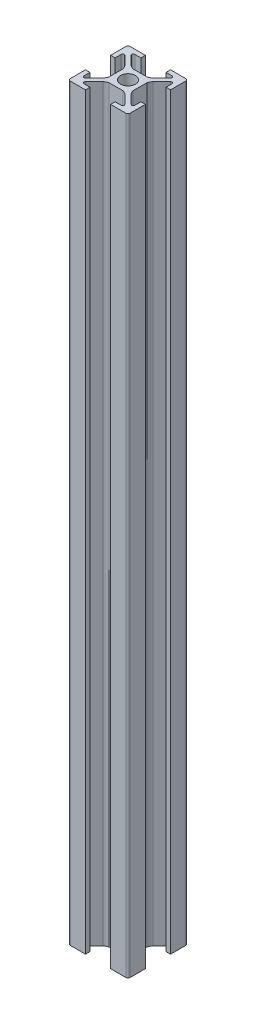
SolidWorks part; units mm, degrees
ref_plane "Front Plane" through (0, 0, 0) normal (0, 0, 1) x (1, 0, 0)
ref_plane "Top Plane" through (0, 0, 0) normal (0, 1, 0) x (1, 0, 0)
ref_plane "Right Plane" through (0, 0, 0) normal (1, 0, 0) x (0, 0, -1)
sketch "Sketch1" plane through (0, 0, 0) normal (0, 1, 0) x (1, 0, 0)
  line L0 (-3.611, 4.6716) -> (-6.5858, 7.6464)
  line L1 (9.25, -10) -> (4.2, -10)
  line L2 (10, -9.25) -> (10, -4.2)
  line L3 (9.25, 10) -> (4.2, 10)
  line L4 (-10, -9.25) -> (-10, -4.2)
  line L5 (10, -10) -> (-10, 10) construction
  line L6 (10, 10) -> (-10, -10) construction
  line L7 (2.2681, -4) -> (-2.2681, -4)
  line L8 (4, -2.2681) -> (4, 2.2681)
  line L9 (2.2681, 4) -> (-2.2681, 4)
  line L10 (-4, -2.2681) -> (-4, 2.2681)
  line L11 (4, -4) -> (-4, 4) construction
  line L12 (4, 4) -> (-4, -4) construction
  line L13 (-6.2322, 8.5) -> (-4.2, 8.5)
  line L14 (-4.2, 8.5) -> (-4.2, 10)
  line L15 (4.6716, 3.611) -> (7.6464, 6.5858)
  line L16 (8.5, 6.2322) -> (8.5, 4.2)
  line L17 (8.5, 4.2) -> (10, 4.2)
  line L18 (4.2, 8.5) -> (4.2, 10)
  line L19 (-8.5, 4.2) -> (-10, 4.2)
  line L20 (-8.5, 6.2322) -> (-8.5, 4.2)
  line L21 (-4.6716, 3.611) -> (-7.6464, 6.5858)
  line L22 (0, 10) -> (0, -10) construction
  line L23 (6.2322, 8.5) -> (4.2, 8.5)
  line L24 (3.611, 4.6716) -> (6.5858, 7.6464)
  line L25 (-55, 0) -> (55, 0) construction
  line L26 (3.611, -4.6716) -> (6.5858, -7.6464)
  line L27 (6.2322, -8.5) -> (4.2, -8.5)
  line L28 (-4.6716, -3.611) -> (-7.6464, -6.5858)
  line L29 (-8.5, -6.2322) -> (-8.5, -4.2)
  line L30 (-8.5, -4.2) -> (-10, -4.2)
  line L31 (4.2, -8.5) -> (4.2, -10)
  line L32 (8.5, -4.2) -> (10, -4.2)
  line L33 (8.5, -6.2322) -> (8.5, -4.2)
  line L34 (4.6716, -3.611) -> (7.6464, -6.5858)
  line L35 (-4.2, -8.5) -> (-4.2, -10)
  line L36 (-6.2322, -8.5) -> (-4.2, -8.5)
  line L37 (2.2681, -4) -> (-2.2681, -4)
  line L38 (10, -10) -> (4.2, -10)
  line L39 (-3.611, -4.6716) -> (-6.5858, -7.6464)
  line L40 (-4.2, 10) -> (-9.25, 10)
  line L41 (-10, 4.2) -> (-10, 9.25)
  line L42 (-4.2, -10) -> (-9.25, -10)
  line L43 (-4.2, -10) -> (-10, -10)
  line L44 (10, 4.2) -> (10, 9.25)
  circle A0 centre (0, 0) radius 2.5
  arc A1 (-8.5, 6.2322) -> (-7.6464, 6.5858) centre (-8, 6.2322) cw
  arc A2 (-6.5858, 7.6464) -> (-6.2322, 8.5) centre (-6.2322, 8) cw
  arc A3 (-3.611, 4.6716) -> (-2.2681, 4) centre (-1.7294, 6.7555) ccw
  arc A4 (-4.6716, 3.611) -> (-4, 2.2681) centre (-6.7555, 1.7294) cw
  arc A5 (4.6716, 3.611) -> (4, 2.2681) centre (6.7555, 1.7294) ccw
  arc A6 (3.611, 4.6716) -> (2.2681, 4) centre (1.7294, 6.7555) cw
  arc A7 (6.5858, 7.6464) -> (6.2322, 8.5) centre (6.2322, 8) ccw
  arc A8 (8.5, 6.2322) -> (7.6464, 6.5858) centre (8, 6.2322) ccw
  arc A9 (8.5, -6.2322) -> (7.6464, -6.5858) centre (8, -6.2322) cw
  arc A10 (6.5858, -7.6464) -> (6.2322, -8.5) centre (6.2322, -8) cw
  arc A11 (3.611, -4.6716) -> (2.2681, -4) centre (1.7294, -6.7555) ccw
  arc A12 (4.6716, -3.611) -> (4, -2.2681) centre (6.7555, -1.7294) cw
  arc A13 (-4.6716, -3.611) -> (-4, -2.2681) centre (-6.7555, -1.7294) ccw
  arc A14 (-3.611, -4.6716) -> (-2.2681, -4) centre (-1.7294, -6.7555) cw
  arc A15 (-6.5858, -7.6464) -> (-6.2322, -8.5) centre (-6.2322, -8) ccw
  arc A16 (-8.5, -6.2322) -> (-7.6464, -6.5858) centre (-8, -6.2322) ccw
  arc A17 (-9.25, -10) -> (-10, -9.25) centre (-9.25, -9.25) cw
  arc A18 (9.25, -10) -> (10, -9.25) centre (9.25, -9.25) ccw
  arc A19 (10, 9.25) -> (9.25, 10) centre (9.25, 9.25) ccw
  arc A20 (-9.25, 10) -> (-10, 9.25) centre (-9.25, 9.25) ccw
  point P0 (0, 0)
  point P18 (-8.5, 7.4393)
  point P24 (-7.4393, 8.5)
  point P50 (7.4393, 8.5)
  point P51 (8.5, 7.4393)
  point P86 (8.5, -7.4393)
  point P87 (7.4393, -8.5)
  point P88 (-7.4393, -8.5)
  point P89 (-8.5, -7.4393)
  dimension "D2" = 5
  dimension "D7" = 0.5
  dimension "D8" = 0.75
  dimension "D1" = 20
  dimension "D3" = 8
  dimension "D4" = 1.5
  dimension "D5" = 1.5
  dimension "D6" = 8.4
extrude "Boss-Extrude1" add sketch "Sketch1" along normal blind 250 contours L40 A20 L41 L19 L20 A1 L21 A4 L10 A13 L28 A16 L29 L30 L4 A17 L42 L35 L36 A15 L39 A14 L7 A11 L26 A10 L27 L31 L1 A18 L2 L32 L33 A9 L34 A12 L8 A5 L15 A8 L16 L17 L44 A19 L3 L18 L23 A7 L24 A6 L9
